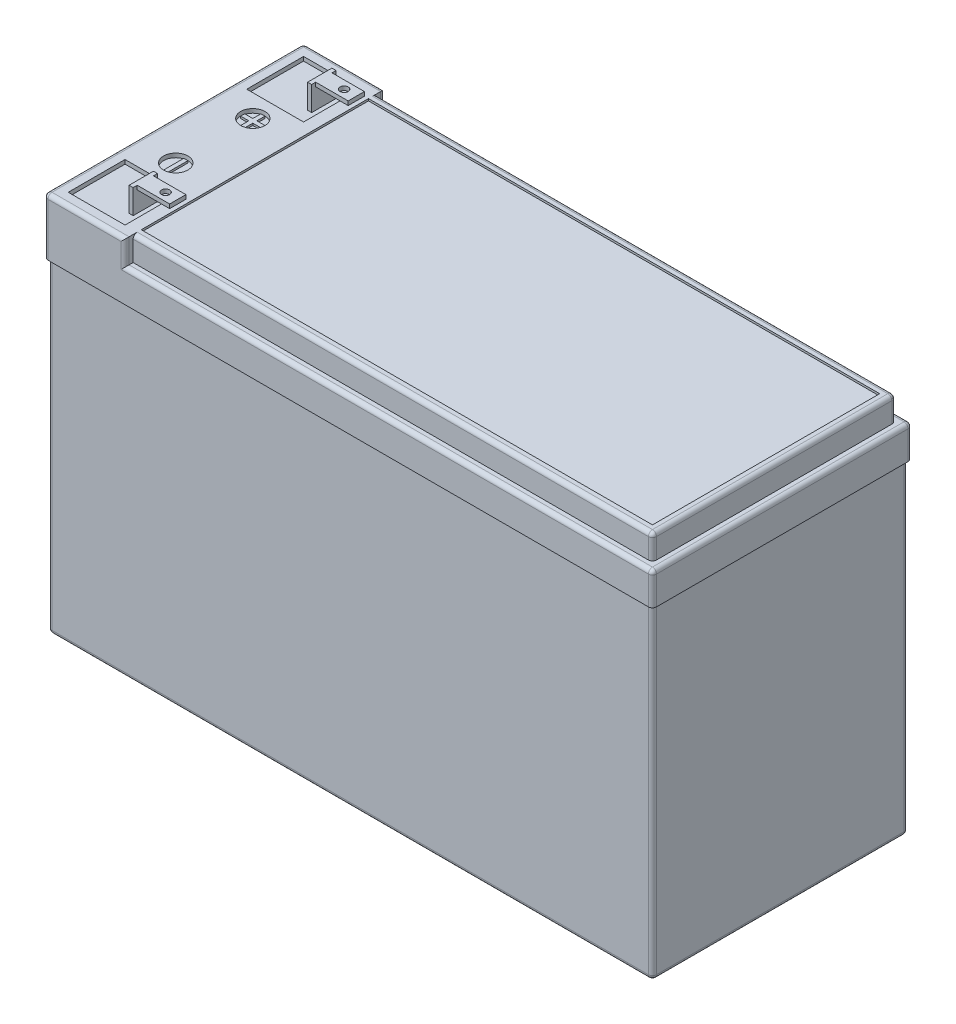
SolidWorks part; units mm, degrees
ref_plane "Front Plane" through (0, 0, 0) normal (0, 0, 1) x (1, 0, 0)
ref_plane "Top Plane" through (0, 0, 0) normal (0, 1, 0) x (1, 0, 0)
ref_plane "Right Plane" through (0, 0, 0) normal (1, 0, 0) x (0, 0, -1)
sketch "Sketch1" plane through (0, 0, 0) normal (0, 1, 0) x (1, 0, 0)
  line L1 (-75, -32) -> (75, -32)
  line L2 (-75, -32) -> (-75, 32)
  line L3 (-75, 32) -> (75, 32)
  line L4 (75, -32) -> (75, 32)
  point P0 (0, 0)
extrude "Boss-Extrude1" add sketch "Sketch1" along normal blind 94
sketch "Sketch2" plane through (75, 0, 0) normal (1, 0, 0) x (0, 0, -1)
  line L0 (32, 94) -> (32, 88)
  line L1 (32, 94) -> (32, 0) construction
  line L2 (32, 94) -> (-32, 94)
  line L3 (-32, 94) -> (-32, 88)
  line L4 (-32, 94) -> (-32, 0) construction
  line L5 (-32, 88) -> (32, 88)
extrude "Cut-Extrude1" cut sketch "Sketch2" against normal blind 2
sketch "Sketch3" plane through (0, 0, -32) normal (0, 0, -1) x (-1, 0, 0)
  line L0 (-73, 88) -> (55, 88)
  line L3 (55, 88) -> (55, 94)
  line L4 (-73, 94) -> (75, 94) construction
  line L5 (55, 94) -> (-73, 94)
  line L6 (-73, 94) -> (-75, 94)
  line L7 (-75, 94) -> (-75, 88)
  line L8 (-75, 88) -> (-73, 88)
extrude "Cut-Extrude2" cut sketch "Sketch3" against normal blind 2
sketch "Sketch4" plane through (0, 0, 32) normal (0, 0, 1) x (1, 0, 0)
  line L0 (75, 88) -> (-55, 88)
  line L3 (-55, 88) -> (-55, 94)
  line L4 (-55, 94) -> (75, 94)
  line L5 (75, 94) -> (75, 88)
extrude "Cut-Extrude3" cut sketch "Sketch4" against normal blind 2
sketch "Sketch5" plane through (0, 94, 0) normal (0, 1, 0) x (1, 0, 0)
  line L1 (-55, 28) -> (-55, -28)
  line L3 (-55, -28) -> (71, -28)
  line L6 (71, -28) -> (71, 28)
  line L7 (71, 28) -> (-55, 28)
extrude "Cut-Extrude4" cut sketch "Sketch5" against normal blind 0.5
sketch "Sketch6" plane through (0, 94, 0) normal (0, 1, 0) x (1, 0, 0)
  line L3 (-72, -29) -> (-72, -15)
  line L5 (-72, -29) -> (-58, -29)
  line L6 (-58, -29) -> (-58, -15)
  line L7 (-72, 29) -> (-58, 29)
  line L8 (-72, 29) -> (-72, 15)
  line L9 (-72, 15) -> (-58, 15)
  line L10 (-58, 29) -> (-58, 15)
  line L11 (-72, -15) -> (-58, -15)
extrude "Cut-Extrude5" cut sketch "Sketch6" against normal blind 1
sketch "Sketch7" plane through (0, 93, 0) normal (0, 1, 0) x (1, 0, 0)
  line L7 (-61, 25) -> (-61, 19)
  line L8 (-61, 25) -> (-60, 25)
  line L9 (-60, 25) -> (-60, 19)
  line L10 (-60, 19) -> (-61, 19)
  line L11 (-61, -25) -> (-60, -25)
  line L12 (-60, -19) -> (-61, -19)
  line L13 (-60, -25) -> (-60, -19)
  line L14 (-61, -25) -> (-61, -19)
extrude "Boss-Extrude2" add sketch "Sketch7" along normal blind 6
sketch "Sketch8" plane through (-60, 0, 0) normal (1, 0, 0) x (0, 0, -1)
  line L3 (-25, 99) -> (-19, 99) construction
  line L4 (-24, 99) -> (-24, 98)
  line L5 (-24, 99) -> (-20, 99)
  line L6 (-24, 98) -> (-20, 98)
  line L7 (-20, 98) -> (-20, 99)
  line L8 (24, 99) -> (24, 98)
  line L9 (24, 99) -> (20, 99)
  line L10 (20, 98) -> (20, 99)
  line L11 (24, 98) -> (20, 98)
extrude "Boss-Extrude3" add sketch "Sketch8" along normal blind 8
sketch "Sketch9" plane through (0, 99, 0) normal (0, 1, 0) x (1, 0, 0)
  circle A0 centre (-55, 22) radius 1
  circle A1 centre (-55, -22) radius 1
extrude "Cut-Extrude6" cut sketch "Sketch9" against normal up to surface (1 mm away) up to face at (-56, 98, 22)
sketch "Sketch13" plane through (75, 0, 0) normal (1, 0, 0) x (0, 0, -1)
  line L1 (32, 88) -> (32, 0) construction
  line L2 (32, 80) -> (-32, 80)
  line L3 (-32, 88) -> (-32, 0) construction
  line L4 (-32, 80) -> (-32, 0)
  line L5 (-32, 0) -> (32, 0)
  line L6 (32, 0) -> (32, 80)
extrude "Cut-Extrude7" cut sketch "Sketch13" against normal blind 0.5
sketch "Sketch14" plane through (0, 0, 32) normal (0, 0, 1) x (1, 0, 0)
  line L0 (74.5, 80) -> (-75, 80)
  line L1 (-75, 94) -> (-75, 0) construction
  line L2 (-75, 80) -> (-75, 0)
  line L3 (-75, 0) -> (74.5, 0)
  line L4 (74.5, 0) -> (74.5, 80)
extrude "Cut-Extrude8" cut sketch "Sketch14" against normal blind 0.5
sketch "Sketch15" plane through (0, 0, -32) normal (0, 0, -1) x (-1, 0, 0)
  line L0 (-74.5, 80) -> (75, 80)
  line L1 (75, 94) -> (75, 0) construction
  line L2 (75, 80) -> (75, 0)
  line L3 (75, 0) -> (-74.5, 0)
  line L4 (-74.5, 0) -> (-74.5, 80)
extrude "Cut-Extrude9" cut sketch "Sketch15" against normal blind 0.5
sketch "Sketch16" plane through (-75, 0, 0) normal (-1, 0, 0) x (0, 0, 1)
  line L0 (31.5, 80) -> (-31.5, 80)
  line L1 (-31.5, 80) -> (-31.5, 0)
  line L2 (-31.5, 0) -> (31.5, 0)
  line L3 (31.5, 0) -> (31.5, 80)
extrude "Cut-Extrude10" cut sketch "Sketch16" against normal blind 0.5
sketch "Sketch17" plane through (0, 94, 0) normal (0, 1, 0) x (1, 0, 0)
  line L3 (-55, 0) -> (-75, 0) construction
  line L4 (-55, 28) -> (-55, -28) construction
  line L5 (-75, 32) -> (-75, -32) construction
  circle A0 centre (-65, 9.5) radius 3
  circle A1 centre (-65, -9.5) radius 3
extrude "Cut-Extrude11" cut sketch "Sketch17" against normal blind 1
sketch "Sketch18" plane through (0, 93, 0) normal (0, 1, 0) x (1, 0, 0)
  line L0 (-55, 0) -> (-75, 0) construction
  line L1 (-55, 28) -> (-55, -28) construction
  line L2 (-75, 32) -> (-75, -32) construction
  line L5 (-65.5, 12) -> (-64.5, 12)
  line L6 (-64.5, 12) -> (-64.5, 10)
  line L7 (-65.5, 12) -> (-65.5, 10)
  line L8 (-65.5, 7) -> (-64.5, 7)
  line L9 (-65.5, -12) -> (-64.5, -12)
  line L10 (-65.5, -7) -> (-64.5, -7)
  line L11 (-65.5, -12) -> (-65.5, -7)
  line L12 (-64.5, -12) -> (-64.5, -7)
  line L13 (-67.5, 10) -> (-65.5, 10)
  line L14 (-62.5, 10) -> (-62.5, 9)
  line L15 (-67.5, 9) -> (-65.5, 9)
  line L16 (-67.5, 10) -> (-67.5, 9)
  line L17 (-64.5, 9) -> (-64.5, 7)
  line L19 (-65.5, 9) -> (-65.5, 7)
  line L20 (-64.5, 10) -> (-62.5, 10)
  line L21 (-64.5, 9) -> (-62.5, 9)
  point P19 (-65, 12)
  point P30 (-62.5, 9.5)
extrude "Boss-Extrude4" add sketch "Sketch18" along normal blind 0.5
fillet "Fillet4" radius 1 8 edges at (0, 0, 31.5) (74.5, 0, 0) (74.5, 40, 31.5) (74.5, 40, -31.5) (0, 0, -31.5) (-74.5, 0, 0) (-74.5, 40, 31.5) (-74.5, 40, -31.5)
fillet "Fillet5" radius 1 17 edges at (-75, 87, 32) (-75, 94, 0) (-55, 91, 32) (-65, 94, 32) (73, 94, 0) (9, 94, 30) (10, 88, 32) (75, 84, 32) (73, 91, 30) (-55, 91, -32) (-65, 94, -32) (-75, 87, -32) (9, 94, -30) (75, 88, 0) (10, 88, -32) (73, 91, -30) (75, 84, -32)
